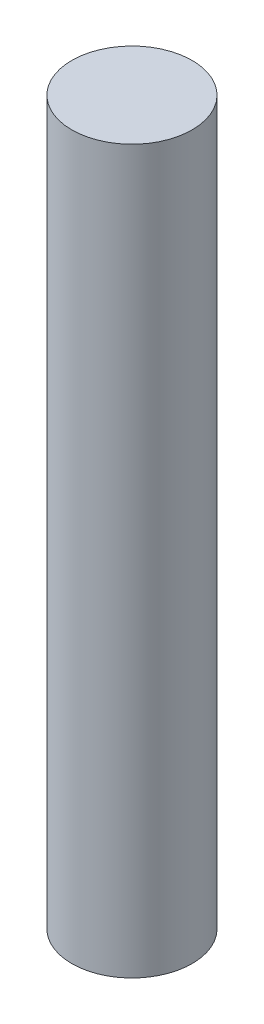
SolidWorks part; units mm, degrees
ref_plane "Front Plane" through (0, 0, 0) normal (0, 0, 1) x (1, 0, 0)
ref_plane "Top Plane" through (0, 0, 0) normal (0, 1, 0) x (1, 0, 0)
ref_plane "Right Plane" through (0, 0, 0) normal (1, 0, 0) x (0, 0, -1)
sketch "Sketch1" plane through (0, 0, 0) normal (0, 1, 0) x (1, 0, 0)
  circle A0 centre (-9.5455, -4.4318) radius 3.75
  dimension "D1" = 7.5
extrude "Boss-Extrude1" add sketch "Sketch1" along normal blind 45
